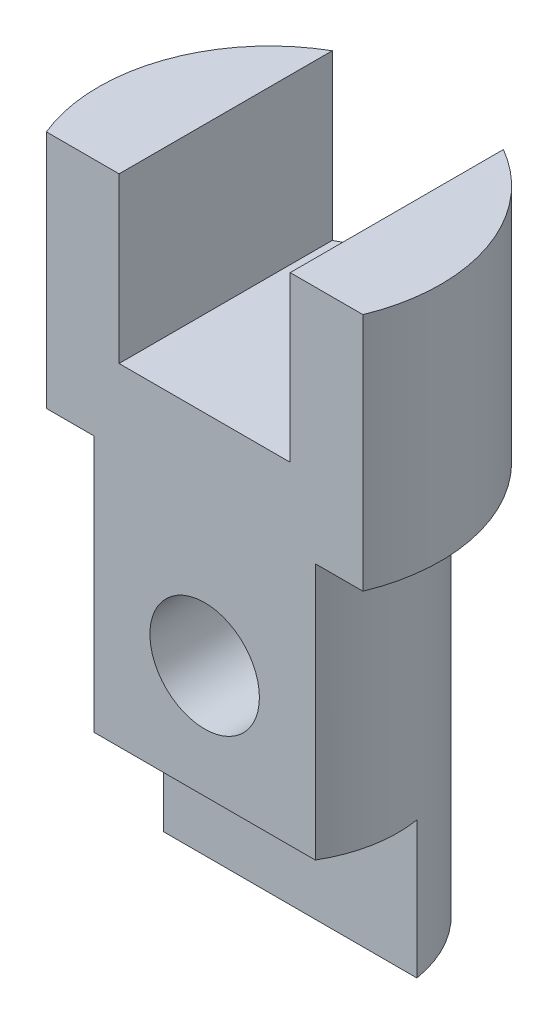
SolidWorks part; units mm, degrees
ref_plane "Front Plane" through (0, 0, 0) normal (0, 0, 1) x (1, 0, 0)
ref_plane "Top Plane" through (0, 0, 0) normal (0, 1, 0) x (1, 0, 0)
ref_plane "Right Plane" through (0, 0, 0) normal (1, 0, 0) x (0, 0, -1)
sketch "Sketch1" plane through (0, 0, 0) normal (0, 1, 0) x (1, 0, 0)
  line L0 (-46.2493, -19) -> (46.2493, -19)
  arc A0 (46.2493, -19) -> (-46.2493, -19) centre (0, 0) ccw
  dimension "D1" = 100
  dimension "D2" = 19
extrude "Boss-Extrude1" add sketch "Sketch1" along normal blind 70
sketch "Sketch2" plane through (0, 70, 0) normal (0, 1, 0) x (1, 0, 0)
  line L0 (-46.2493, -19) -> (46.2493, -19) construction
  line L1 (-25, -19) -> (25, -19)
  line L2 (-25, -19) -> (-25, 55.6671)
  line L3 (-25, 55.6671) -> (25, 55.6671)
  line L4 (25, -19) -> (25, 55.6671)
  line L5 (0, 0) -> (0, 30.3063) construction
  dimension "D1" = 50
extrude "Cut-Extrude1" cut sketch "Sketch2" against normal blind 48
sketch "Sketch3" plane through (0, 0, 0) normal (0, -1, 0) x (1, 0, 0)
  line L1 (46.2493, 19) -> (-46.2493, 19)
  line L2 (32.3303, 19) -> (-32.3303, 19)
  arc A0 (-32.3303, 19) -> (32.3303, 19) centre (0, 0) ccw
  arc A2 (-46.2493, 19) -> (46.2493, 19) centre (0, 0) ccw
  dimension "D1" = 75
  dimension "D2" = 0
extrude "Boss-Extrude2" add sketch "Sketch3" along normal blind 75
sketch "Sketch4" plane through (0, -75, 0) normal (0, -1, 0) x (1, 0, 0)
  line L0 (-37.0169, -6) -> (37.0169, -6)
  line L1 (32.3303, 19) -> (-32.3303, 19)
  arc A1 (-32.3303, 19) -> (32.3303, 19) centre (0, 0) ccw
  arc A2 (-37.0169, -6) -> (37.0169, -6) centre (0, 0) ccw
  dimension "D1" = 0
extrude "Boss-Extrude3" add sketch "Sketch4" along normal blind 40
sketch "Sketch5" plane through (0, 0, 19) normal (0, 0, 1) x (1, 0, 0)
  line L0 (0, 0) -> (0, -53.5715) construction
  line L1 (32.3303, -75) -> (-32.3303, -75) construction
  circle A0 centre (0, -42) radius 16
  dimension "D1" = 32
  dimension "D2" = 33
extrude "Cut-Extrude2" cut sketch "Sketch5" against normal through all
